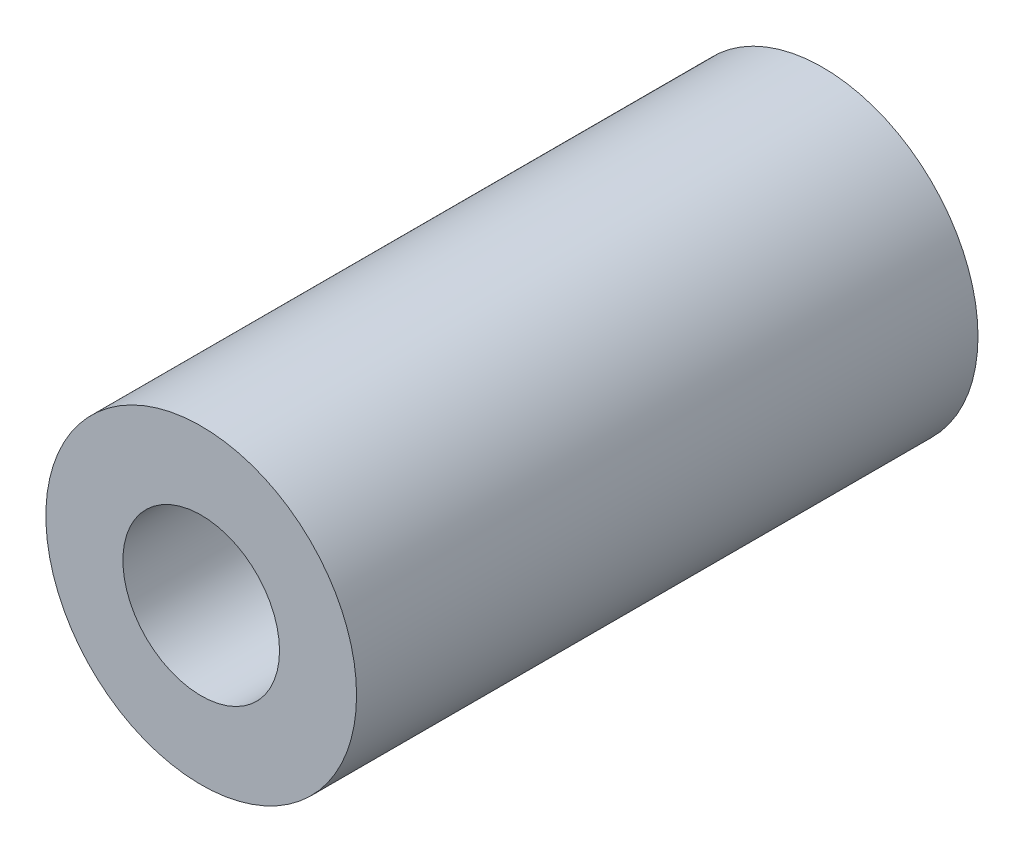
SolidWorks part; units mm, degrees
ref_plane "Front Plane" through (0, 0, 0) normal (0, 0, 1) x (1, 0, 0)
ref_plane "Top Plane" through (0, 0, 0) normal (0, 1, 0) x (1, 0, 0)
ref_plane "Right Plane" through (0, 0, 0) normal (1, 0, 0) x (0, 0, -1)
sketch "Sketch1" plane through (0, 0, 0) normal (0, 0, 1) x (1, 0, 0)
  circle A0 centre (0, 0) radius 6.35
  circle A1 centre (0, 0) radius 3.2004
  dimension "OD" = 12.7
  dimension "ID" = 6.4008
extrude "Extrude1" add sketch "Sketch1" along normal mid plane 25.4
sketch "Sketch2" plane through (0, 0, 0) normal (1, 0, 0) x (0, 0, -1)
  line L0 (-12.7, -3.2004) -> (12.7, -3.2004) construction
  line L3 (12.7, 3.2004) -> (-12.7, 3.2004) construction
  line L5 (-12.7, -3.2004) -> (12.7, -3.2004)
  line L6 (12.7, 3.2004) -> (-12.7, 3.2004)
sketch "Sketch4" plane through (0, 0, 12.7) normal (0, 0, 1) x (1, 0, 0)
  line L0 (0, 0) -> (-2.263, 2.263)
  line L1 (0, -3.4925) -> (0, 3.4925) construction
  circle A0 centre (0, 0) radius 3.2004 construction
  dimension "D1" = 45
